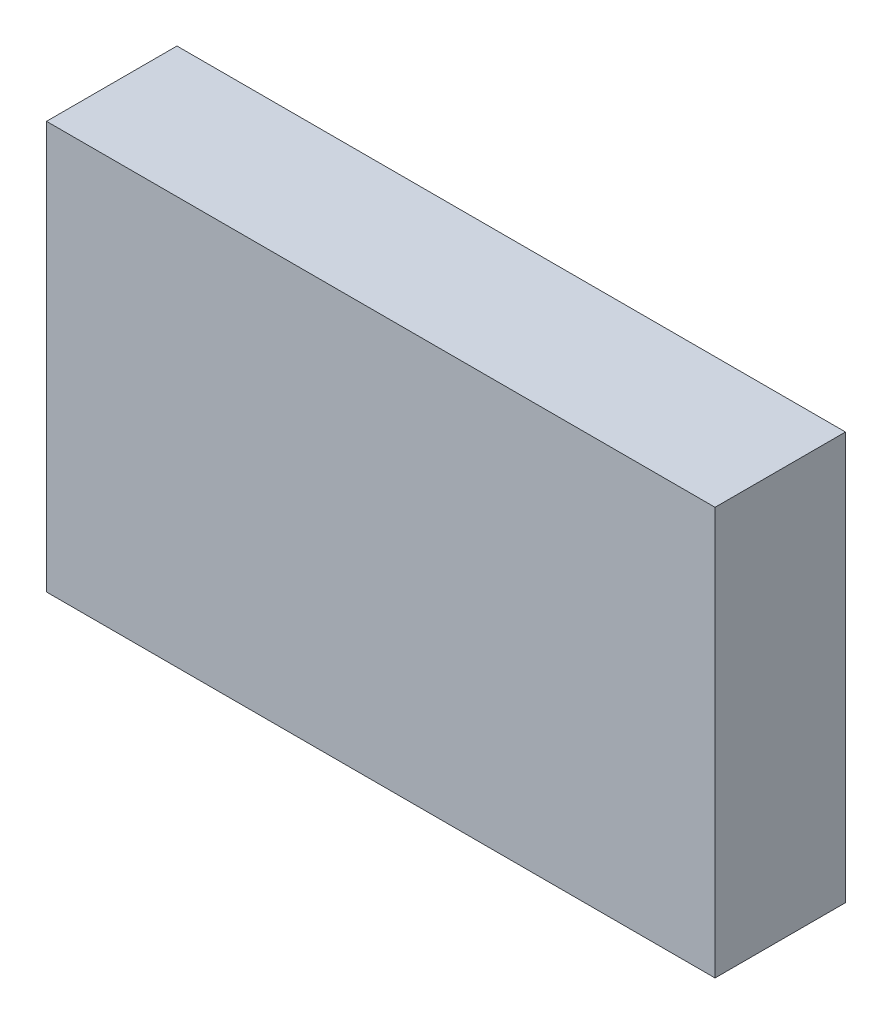
SolidWorks part; units mm, degrees
ref_plane "前视基准面" through (0, 0, 0) normal (0, 0, 1) x (1, 0, 0)
ref_plane "上视基准面" through (0, 0, 0) normal (0, 1, 0) x (1, 0, 0)
ref_plane "右视基准面" through (0, 0, 0) normal (1, 0, 0) x (0, 0, -1)
ref_plane "基准面4" through (0, 0, 16) normal (0, 0, 1) x (1, 0, 0)
sketch "草图1" plane through (0, 0, 16) normal (0, 0, 1) x (1, 0, 0)
  line L0 (124.9067, 43.6904) -> (124.9067, -6.3096)
  line L1 (124.9067, -6.3096) -> (206.9067, -6.3096)
  line L2 (206.9067, -6.3096) -> (206.9067, 43.6904)
  line L3 (206.9067, 43.6904) -> (124.9067, 43.6904)
extrude "凸台-拉伸1" add sketch "草图1" against normal blind 16
